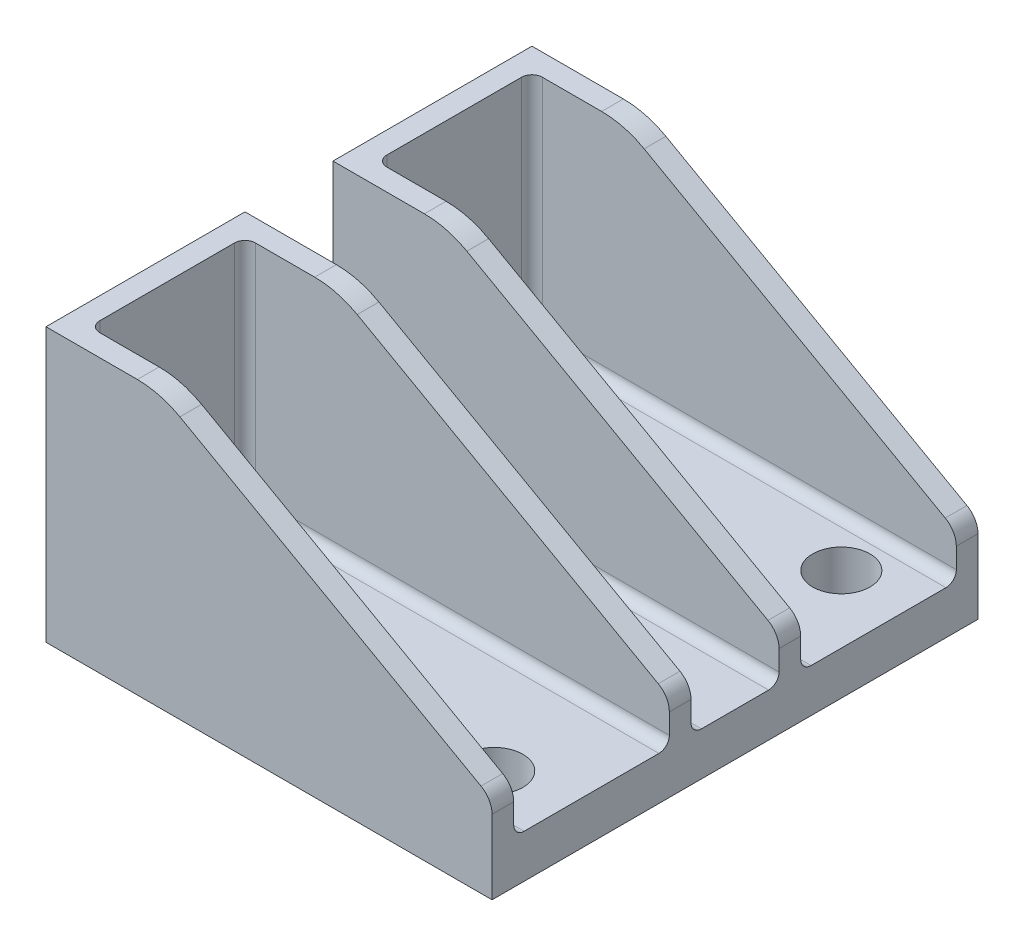
SolidWorks part; units mm, degrees
ref_plane "Front Plane" through (0, 0, 0) normal (0, 0, 1) x (1, 0, 0)
ref_plane "Top Plane" through (0, 0, 0) normal (0, 1, 0) x (1, 0, 0)
ref_plane "Right Plane" through (0, 0, 0) normal (1, 0, 0) x (0, 0, -1)
sketch "Sketch1" plane through (0, 0, 0) normal (0, 1, 0) x (1, 0, 0)
  line L0 (-17.9521, 0) -> (17.9521, 0) construction
  line L3 (7.9997, 17.78) -> (40.64, 17.78)
  line L4 (40.64, -17.78) -> (40.64, 17.78)
  line L5 (7.9998, -17.78) -> (40.64, -17.78)
  line L6 (0, -19.558) -> (0, 19.558) construction
  line L7 (7.9997, 17.78) -> (7.9998, -17.78)
  circle A0 centre (35.7188, 12.7) radius 2.1
  circle A1 centre (35.7188, -12.7) radius 2.1
  dimension "D3" = 4.2
  dimension "D1" = 12.7
  dimension "D2" = 35.7188
  dimension "D4" = 40.64
  dimension "D5" = 27.719
extrude "Boss-Extrude2" add sketch "Sketch1" along normal blind 3.175
sketch "Sketch2" plane through (0, 0, 17.78) normal (0, 0, 1) x (1, 0, 0)
  line L0 (17.7989, 19.1858) -> (39.8302, 6.8051)
  line L1 (7.9997, 3.175) -> (40.64, 3.175)
  line L2 (7.9997, 3.175) -> (7.9997, 20)
  line L3 (11.5875, 20) -> (14.688, 20)
  line L4 (40.64, 3.175) -> (40.64, 5.4211)
  line L5 (11.5875, 20) -> (7.9997, 20)
  arc A0 (17.7989, 19.1858) -> (14.688, 20) centre (14.688, 13.65) ccw
  arc A2 (39.8302, 6.8051) -> (40.64, 5.4211) centre (39.0525, 5.4211) cw
  point P11 (7.9997, 20)
  dimension "D3" = 6.35
  dimension "D2" = 1.5875
  dimension "D1" = 16.825
extrude "Boss-Extrude3" add sketch "Sketch2" against normal blind 1.5875
ref_plane "Plane4" through (0, 0, 10.5) normal (0, 0, 1) x (1, 0, 0)
mirror "Mirror1" about plane through (0, 0, 10.5) normal (0, 0, 1) of "Boss-Extrude3"
sketch "Sketch4" plane through (7.9998, 0, 0) normal (-1, 0, 0) x (0, 0, 1)
  line L0 (10.5, -11) -> (10.5, 11) construction
  line L1 (16.1925, 20) -> (4.8075, 20)
  line L2 (16.1925, 20) -> (16.1925, 3.175)
  line L3 (16.1925, 3.175) -> (4.8075, 3.175)
  line L4 (4.8075, 20) -> (4.8075, 3.175)
  line L5 (17.9521, 0) -> (-17.9521, 0) construction
  circle A0 centre (10.5, 10) radius 2.45
  dimension "D2" = 4.9
  dimension "D1" = 10
extrude "Boss-Extrude4" add sketch "Sketch4" against normal blind 1.5875
mirror "Mirror2" about plane through (0, 0, 0) normal (0, 0, 1) of "Boss-Extrude3", "Mirror1", "Boss-Extrude4"
fillet "Fillet1" radius 0.762 1 edges at (9.5873, 11.5875, 4.8075)
fillet "Fillet2" radius 0.762 1 edges at (9.5873, 11.5875, 16.1925)
fillet "Fillet6" radius 0.762 1 edges at (24.3199, 3.175, 3.22)
fillet "Fillet7" radius 0.762 11 edges at (25.4946, 3.175, 16.1925) (9.8104, 3.175, 15.9693) (9.5873, 3.175, 10.5) (9.8104, 3.175, 5.0307) (9.5873, 11.5875, -4.8075) (9.5873, 3.175, -10.5) (25.1136, 3.175, -16.1925) (9.5873, 11.5875, -16.1925) (25.4946, 3.175, 4.8075) (25.1136, 3.175, -4.8075) (24.3199, 3.175, -3.22)
